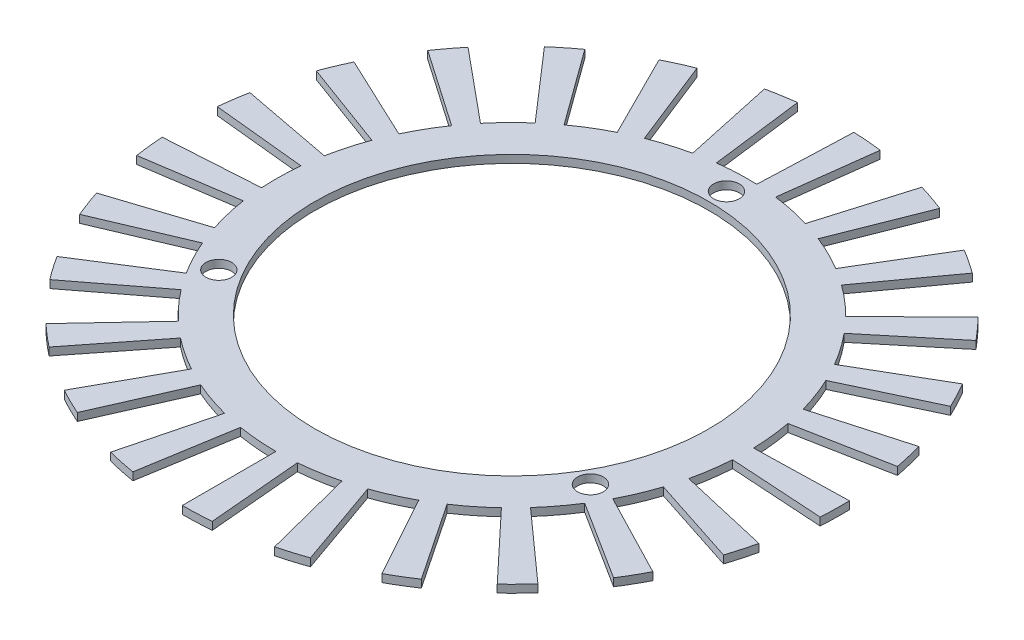
SolidWorks part; units mm, degrees
material "AISI 1010 Steel, hot rolled bar"
ref_plane "Front Plane" through (0, 0, 0) normal (0, 0, 1) x (1, 0, 0)
ref_plane "Top Plane" through (0, 0, 0) normal (0, 1, 0) x (1, 0, 0)
ref_plane "Right Plane" through (0, 0, 0) normal (1, 0, 0) x (0, 0, -1)
sketch "Sketch1" plane through (0, 0, 0) normal (0, 1, 0) x (1, 0, 0)
  circle A0 centre (0, 0) radius 25.25
  dimension "D1" = 50.5
extrude "Extrude-Thin1" add sketch "Sketch1" against normal blind 1 thin
sketch "Sketch2" plane through (0, 0, 0) normal (0, 1, 0) x (1, 0, 0)
  line L0 (0, -30.25) -> (0, 30.25) construction
  line L1 (0, 0) -> (23.8157, -13.75) construction
  line L2 (0, 0) -> (-23.8157, -13.75) construction
  circle A0 centre (0, 27.5) radius 1.65
  circle A1 centre (0, 0) radius 30.25 construction
  circle A4 centre (0, 0) radius 27.5 construction
  circle A7 centre (23.8157, -13.75) radius 1.65
  circle A8 centre (-23.8157, -13.75) radius 1.65
  dimension "D1" = 55
  dimension "D2" = 3.3
  dimension "D3" = 120
  dimension "D4" = 120
extrude "Cut-Extrude3" cut sketch "Sketch2" against normal blind 10
sketch "Sketch5" plane through (0, -1, 0) normal (0, -1, 0) x (1, 0, 0)
  line L0 (0, 0) -> (0, 35.9971) construction
  line L1 (0, 0) -> (2.9726, 33.977) construction
  line L2 (0, 42.25) -> (0, 30.25)
  line L3 (2.6365, 30.1349) -> (3.6823, 42.0892)
  line L4 (10.5071, 40.9226) -> (7.5229, 29.2996)
  line L5 (10.0479, 28.5325) -> (14.0338, 39.8512)
  line L6 (20.3541, 37.024) -> (14.573, 26.5083)
  line L7 (16.8279, 25.1373) -> (23.5035, 35.1091)
  line L8 (28.9221, 30.7989) -> (20.7075, 22.0513)
  line L9 (22.5506, 20.1626) -> (31.4964, 28.161)
  line L10 (35.6729, 22.6387) -> (25.5409, 16.2088)
  line L11 (26.8564, 13.921) -> (37.5102, 19.4434)
  line L12 (40.1821, 13.056) -> (28.7695, 9.3478)
  line L13 (29.4747, 6.8048) -> (41.1671, 9.5042)
  line L14 (42.1666, 2.6529) -> (30.1903, 1.8994)
  line L15 (30.241, -0.7391) -> (42.2374, -1.0323)
  line L16 (41.5016, -7.9169) -> (29.7142, -5.6683)
  line L17 (29.1071, -8.2365) -> (40.6537, -11.5038)
  line L18 (38.2289, -17.9892) -> (27.371, -12.8798)
  line L19 (26.1443, -15.2164) -> (36.5156, -21.2526)
  line L20 (32.5542, -26.9312) -> (23.308, -19.2821)
  line L21 (21.5388, -21.2401) -> (30.0831, -29.666)
  line L22 (24.8339, -34.181) -> (17.7805, -24.4728)
  line L23 (15.5799, -25.9293) -> (21.7604, -36.2153)
  line L24 (15.5533, -39.2831) -> (11.1358, -28.1257)
  line L25 (8.6421, -28.9893) -> (12.0703, -40.4891)
  line L26 (5.2953, -41.9168) -> (3.7913, -30.0115)
  line L27 (1.1612, -30.2277) -> (1.6219, -42.2189)
  line L28 (-5.2953, -41.9168) -> (-3.7913, -30.0115)
  line L29 (-6.3926, -29.5668) -> (-8.9285, -41.2958)
  line L30 (-15.5533, -39.2831) -> (-11.1358, -28.1257)
  line L31 (-13.5447, -27.0482) -> (-18.9178, -37.778)
  line L32 (-24.8339, -34.181) -> (-17.7805, -24.4728)
  line L33 (-19.8458, -22.83) -> (-27.7185, -31.8865)
  line L34 (-32.5542, -26.9312) -> (-23.308, -19.2821)
  line L35 (-24.8999, -17.1773) -> (-34.7775, -23.9914)
  line L36 (-38.2289, -17.9892) -> (-27.371, -12.8798)
  line L37 (-28.3894, -10.4453) -> (-39.6513, -14.5888)
  line L38 (-41.5016, -7.9169) -> (-29.7142, -5.6683)
  line L39 (-30.0951, -3.057) -> (-42.0337, -4.2696)
  line L40 (-42.1666, 2.6529) -> (-30.1903, 1.8994)
  line L41 (-29.9099, 4.5234) -> (-41.775, 6.3179)
  line L42 (-40.1821, 13.056) -> (-28.7695, 9.3478)
  line L43 (-27.8453, 11.8196) -> (-38.8913, 16.5084)
  line L44 (-35.6729, 22.6387) -> (-25.5409, 16.2088)
  line L45 (-24.031, 18.3731) -> (-33.564, 25.6616)
  line L46 (-28.9221, 30.7989) -> (-20.7075, 22.0513)
  line L47 (-18.7069, 23.7722) -> (-26.1278, 33.2025)
  line L48 (-20.3541, 37.024) -> (-14.573, 26.5083)
  line L49 (-12.2072, 27.6775) -> (-17.0498, 38.657)
  line L50 (-10.5071, 40.9226) -> (-7.5229, 29.2996)
  line L51 (-4.9406, 29.8438) -> (-6.9005, 41.6827)
  circle A0 centre (0, 0) radius 30.25 construction
  arc A1 (2.6365, 30.1349) -> (0, 30.25) centre (0, 0) ccw
  arc A2 (3.6823, 42.0892) -> (0, 42.25) centre (0, 0) ccw
  arc A3 (14.0338, 39.8512) -> (10.5071, 40.9226) centre (0, 0) ccw
  arc A4 (10.0479, 28.5325) -> (7.5229, 29.2996) centre (0, 0) ccw
  arc A5 (23.5035, 35.1091) -> (20.3541, 37.024) centre (0, 0) ccw
  arc A6 (16.8279, 25.1373) -> (14.573, 26.5083) centre (0, 0) ccw
  arc A7 (31.4964, 28.161) -> (28.9221, 30.7989) centre (0, 0) ccw
  arc A8 (22.5506, 20.1626) -> (20.7075, 22.0513) centre (0, 0) ccw
  arc A9 (37.5102, 19.4434) -> (35.6729, 22.6387) centre (0, 0) ccw
  arc A10 (26.8564, 13.921) -> (25.5409, 16.2088) centre (0, 0) ccw
  arc A11 (41.1671, 9.5042) -> (40.1821, 13.056) centre (0, 0) ccw
  arc A12 (29.4747, 6.8048) -> (28.7695, 9.3478) centre (0, 0) ccw
  arc A13 (42.2374, -1.0323) -> (42.1666, 2.6529) centre (0, 0) ccw
  arc A14 (30.241, -0.7391) -> (30.1903, 1.8994) centre (0, 0) ccw
  arc A15 (40.6537, -11.5038) -> (41.5016, -7.9169) centre (0, 0) ccw
  arc A16 (29.1071, -8.2365) -> (29.7142, -5.6683) centre (0, 0) ccw
  arc A17 (36.5156, -21.2526) -> (38.2289, -17.9892) centre (0, 0) ccw
  arc A18 (26.1443, -15.2164) -> (27.371, -12.8798) centre (0, 0) ccw
  arc A19 (30.0831, -29.666) -> (32.5542, -26.9312) centre (0, 0) ccw
  arc A20 (21.5388, -21.2401) -> (23.308, -19.2821) centre (0, 0) ccw
  arc A21 (21.7604, -36.2153) -> (24.8339, -34.181) centre (0, 0) ccw
  arc A22 (15.5799, -25.9293) -> (17.7805, -24.4728) centre (0, 0) ccw
  arc A23 (12.0703, -40.4891) -> (15.5533, -39.2831) centre (0, 0) ccw
  arc A24 (8.6421, -28.9893) -> (11.1358, -28.1257) centre (0, 0) ccw
  arc A25 (1.6219, -42.2189) -> (5.2953, -41.9168) centre (0, 0) ccw
  arc A26 (1.1612, -30.2277) -> (3.7913, -30.0115) centre (0, 0) ccw
  arc A27 (-8.9285, -41.2958) -> (-5.2953, -41.9168) centre (0, 0) ccw
  arc A28 (-6.3926, -29.5668) -> (-3.7913, -30.0115) centre (0, 0) ccw
  arc A29 (-18.9178, -37.778) -> (-15.5533, -39.2831) centre (0, 0) ccw
  arc A30 (-13.5447, -27.0482) -> (-11.1358, -28.1257) centre (0, 0) ccw
  arc A31 (-27.7185, -31.8865) -> (-24.8339, -34.181) centre (0, 0) ccw
  arc A32 (-19.8458, -22.83) -> (-17.7805, -24.4728) centre (0, 0) ccw
  arc A33 (-34.7775, -23.9914) -> (-32.5542, -26.9312) centre (0, 0) ccw
  arc A34 (-24.8999, -17.1773) -> (-23.308, -19.2821) centre (0, 0) ccw
  arc A35 (-39.6513, -14.5888) -> (-38.2289, -17.9892) centre (0, 0) ccw
  arc A36 (-28.3894, -10.4453) -> (-27.371, -12.8798) centre (0, 0) ccw
  arc A37 (-42.0337, -4.2696) -> (-41.5016, -7.9169) centre (0, 0) ccw
  arc A38 (-30.0951, -3.057) -> (-29.7142, -5.6683) centre (0, 0) ccw
  arc A39 (-41.775, 6.3179) -> (-42.1666, 2.6529) centre (0, 0) ccw
  arc A40 (-29.9099, 4.5234) -> (-30.1903, 1.8994) centre (0, 0) ccw
  arc A41 (-38.8913, 16.5084) -> (-40.1821, 13.056) centre (0, 0) ccw
  arc A42 (-27.8453, 11.8196) -> (-28.7695, 9.3478) centre (0, 0) ccw
  arc A43 (-33.564, 25.6616) -> (-35.6729, 22.6387) centre (0, 0) ccw
  arc A44 (-24.031, 18.3731) -> (-25.5409, 16.2088) centre (0, 0) ccw
  arc A45 (-26.1278, 33.2025) -> (-28.9221, 30.7989) centre (0, 0) ccw
  arc A46 (-18.7069, 23.7722) -> (-20.7075, 22.0513) centre (0, 0) ccw
  arc A47 (-17.0498, 38.657) -> (-20.3541, 37.024) centre (0, 0) ccw
  arc A48 (-12.2072, 27.6775) -> (-14.573, 26.5083) centre (0, 0) ccw
  arc A49 (-6.9005, 41.6827) -> (-10.5071, 40.9226) centre (0, 0) ccw
  arc A50 (-4.9406, 29.8438) -> (-7.5229, 29.2996) centre (0, 0) ccw
  point P87 (0, 0)
  dimension "D2" = 12
  dimension "D1" = 5
  dimension "D3" = 25
extrude "Boss-Extrude1" add sketch "Sketch5" against normal blind 1
